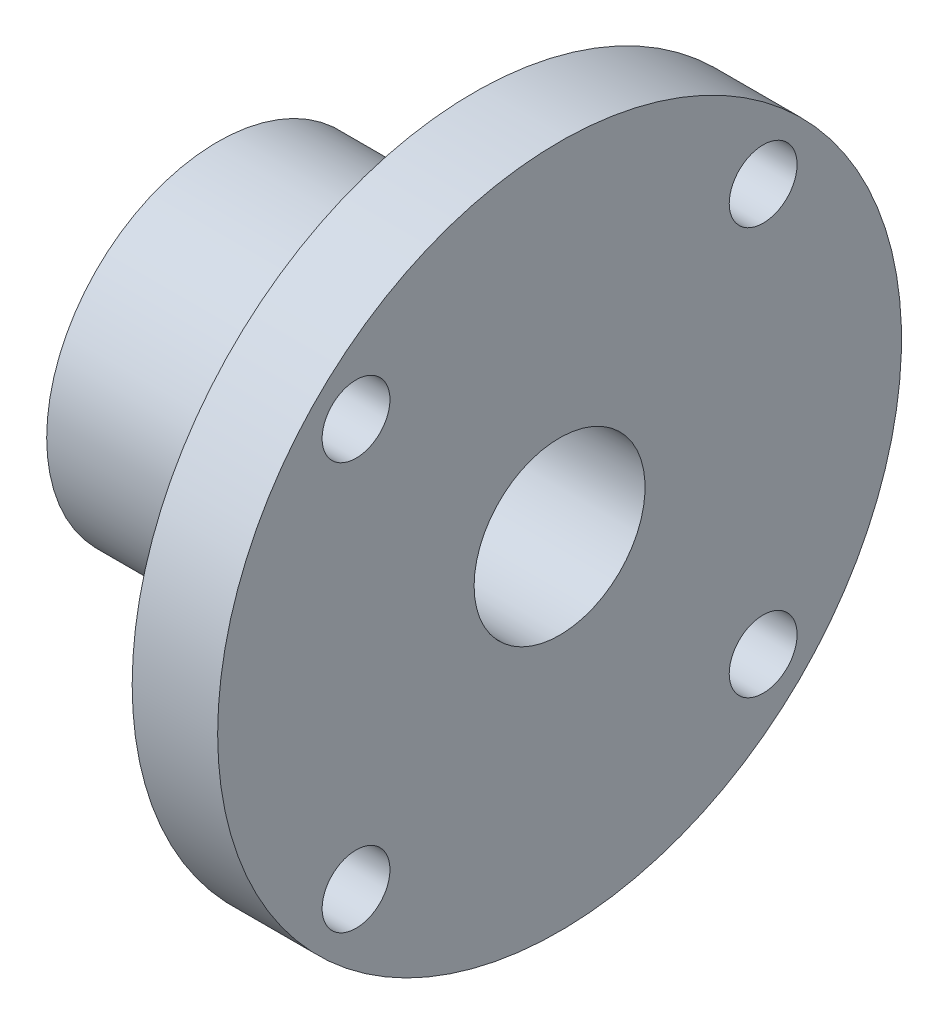
SolidWorks part; units mm, degrees
material "Plain Carbon Steel"
ref_plane "Front Plane" through (0, 0, 0) normal (0, 0, 1) x (1, 0, 0)
ref_plane "Top Plane" through (0, 0, 0) normal (0, 1, 0) x (1, 0, 0)
ref_plane "Right Plane" through (0, 0, 0) normal (1, 0, 0) x (0, 0, -1)
sketch "Sketch2" plane through (0, 0, 0) normal (0, 0, 1) x (1, 0, 0)
  line L0 (-12.3104, 0) -> (14.3681, 0) construction
  line L1 (-16, -4) -> (0, -4)
  line L2 (0, -4) -> (0, -16)
  line L3 (0, -16) -> (-4, -16)
  line L4 (-4, -16) -> (-4, -8)
  line L5 (-4, -8) -> (-16, -8)
  line L6 (-16, -8) -> (-16, -4)
  dimension "D1" = 16
  dimension "D2" = 8
  dimension "D3" = 4
  dimension "D4" = 4
  dimension "D5" = 16
revolve "Revolve1" add sketch "Sketch2" angle 360 about L0
sketch "Sketch3" plane through (-4, 0, 0) normal (-1, 0, 0) x (0, 0, 1)
  line L1 (-9.525, -9.525) -> (9.525, -9.525) construction
  line L2 (-9.525, -9.525) -> (-9.525, 9.525) construction
  line L3 (-9.525, 9.525) -> (9.525, 9.525) construction
  line L4 (9.525, -9.525) -> (9.525, 9.525) construction
  line L5 (-9.525, -9.525) -> (9.525, 9.525) construction
  line L6 (-9.525, 9.525) -> (9.525, -9.525) construction
  circle A0 centre (-9.525, 9.525) radius 1.5875
  circle A1 centre (-9.525, -9.525) radius 1.5875
  circle A2 centre (9.525, -9.525) radius 1.5875
  circle A3 centre (9.525, 9.525) radius 1.5875
  point P0 (0, 0)
  dimension "D3" = 3.175
  dimension "D4" = 3.175
  dimension "D5" = 3.175
  dimension "D6" = 3.175
  dimension "D1" = 19.05
  dimension "D2" = 19.05
extrude "Cut-Extrude1" cut sketch "Sketch3" against normal up to next
equation "\"D1@Sketch2\" = 16mm"
equation "\"D2@Sketch2\" = 0.49/2"
equation "\"D5@Sketch2\"=0.475"
equation "\"D4@Sketch2\"=0.08"
equation "\"D3@Sketch3\"=1/8"
equation "\"D6@Sketch3\"=0.125"
